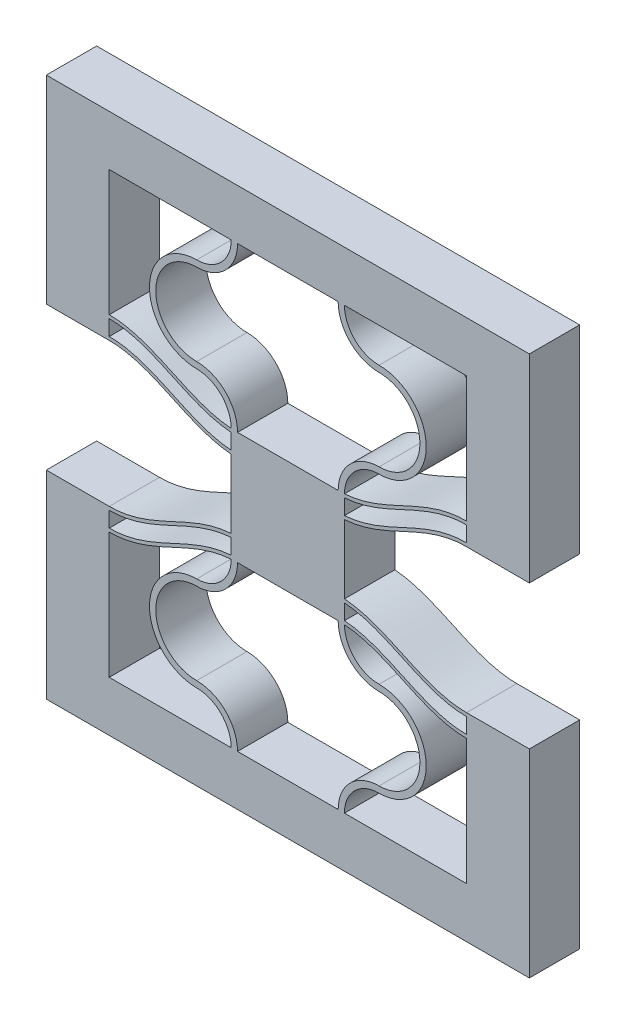
SolidWorks part; units mm, degrees
ref_plane "Front Plane" through (0, 0, 0) normal (0, 0, 1) x (1, 0, 0)
ref_plane "Top Plane" through (0, 0, 0) normal (0, 1, 0) x (1, 0, 0)
ref_plane "Right Plane" through (0, 0, 0) normal (1, 0, 0) x (0, 0, -1)
sketch "Sketch1" plane through (0, 0, 0) normal (0, 0, 1) x (1, 0, 0)
  line L4 (0, 10) -> (0, 0)
  line L5 (10.2, 0) -> (10.2, 13) construction
  line L6 (10.2, 13) -> (10.2, 15.9822) construction
  line L17 (9.7, 0) -> (0, 0)
  line L18 (10.7, 0) -> (20.4, 0)
  line L19 (20.4, 0) -> (20.4, 10)
  line L20 (10.7001, 13.2522) -> (10.7001, 14.4822)
  line L21 (9.6999, 13.2522) -> (9.6999, 14.4822)
  line L22 (10.7001, 14.7522) -> (10.7001, 15.9822)
  line L23 (10.7001, 15.9822) -> (9.6999, 15.9822)
  line L24 (9.6999, 15.9822) -> (9.6999, 14.7522)
  line L31 (-5, 11.77) -> (-5, -4)
  line L32 (-5, -4) -> (25.4, -4)
  line L33 (25.4, -4) -> (25.4, 11.77)
  line L34 (0, 10.27) -> (0, 11.5)
  line L36 (-5, 11.77) -> (0, 11.77)
  line L37 (25.4, 11.77) -> (20.4, 11.77)
  line L38 (20.4, 10.27) -> (20.4, 11.5)
  arc A0 (10.2, 13) -> (6.95, 9.75) centre (6.95, 13) cw
  arc A1 (6.95, 9.75) -> (6.95, 3.25) centre (6.95, 6.5) ccw
  arc A2 (6.95, 3.25) -> (10.2, 0) centre (6.95, 0) cw
  arc A3 (9.6999, 12.9822) -> (6.95, 10.25) centre (6.95, 13) cw
  arc A4 (6.95, 10.25) -> (6.95, 2.75) centre (6.95, 6.5) ccw
  arc A5 (6.95, 2.75) -> (9.7, 0) centre (6.95, 0) cw
  arc A6 (9.7, 13) -> (6.95, 10.25) centre (6.95, 13) cw construction
  arc A7 (13.45, 3.25) -> (10.2, 0) centre (13.45, 0) ccw
  arc A8 (13.45, 2.75) -> (10.7, 0) centre (13.45, 0) ccw
  arc A9 (13.45, 9.75) -> (13.45, 3.25) centre (13.45, 6.5) cw
  arc A10 (13.45, 10.25) -> (13.45, 2.75) centre (13.45, 6.5) cw
  arc A11 (10.7001, 12.9822) -> (13.45, 10.25) centre (13.45, 13) ccw
  arc A12 (10.2, 13) -> (13.45, 9.75) centre (13.45, 13) ccw
  spline S0 degree 4 poles (-2.0403, 10.5565) (-1.977, 10.5394) (-1.8508, 10.5065) (-1.6651, 10.4606) (-1.4028, 10.4071) (-1.1002, 10.3505) (-0.7494, 10.3082) (-0.4826, 10.2809) (-0.0963, 10.2698) (0.0504, 10.2691) (0.3002, 10.2751) (0.4954, 10.2862) (0.6898, 10.3027) (0.8874, 10.3246) (1.1319, 10.3584) (1.4241, 10.409) (1.7623, 10.4818) (2.2204, 10.602) (2.7465, 10.7686) (3.2637, 10.961) (3.7735, 11.1717) (4.2072, 11.3616) (4.5674, 11.5244) (4.9265, 11.6897) (5.2852, 11.8557) (5.734, 12.0622) (6.4147, 12.3676) (7.1961, 12.6896) (8.0933, 12.9875) (9.0168, 13.1885) (9.8039, 13.2774) (10.5961, 13.2774) (11.3832, 13.1885) (12.3067, 12.9875) (13.2039, 12.6896) (13.9853, 12.3676) (14.666, 12.0622) (15.1148, 11.8557) (15.4735, 11.6897) (15.8327, 11.5244) (16.1927, 11.3616) (16.6268, 11.1717) (17.1359, 10.961) (17.7469, 10.7341) (18.3679, 10.5443) (18.928, 10.4147) (19.4122, 10.3342) (19.7634, 10.2959) (20.0425, 10.2765) (20.3499, 10.2691) (20.4953, 10.2698) (20.8095, 10.2786) (21.0299, 10.2972) (21.302, 10.325) (21.5503, 10.3617) (21.8089, 10.4071) (22.0615, 10.4606) (22.2517, 10.5065) (22.3773, 10.5394) (22.4399, 10.5565) knots 0 0 0 0 0 0.010159 0.020319 0.030478 0.040638 0.060704 0.070737 0.080771 0.088497 0.096222 0.103948 0.111674 0.1194 0.127126 0.142578 0.15803 0.173482 0.201155 0.228828 0.24428 0.259732 0.275184 0.290636 0.306088 0.32154 0.352443 0.407289 0.438193 0.469096 0.5 0.530904 0.561807 0.592711 0.647557 0.67846 0.693912 0.709364 0.724816 0.740268 0.75572 0.771172 0.798845 0.826518 0.857422 0.872874 0.888326 0.903778 0.911503 0.919229 0.929263 0.939296 0.949329 0.959362 0.969522 0.979681 0.989841 1 1 1 1 1 construction
  spline S1 degree 4 poles (0, 10.27) (0.0414, 10.27) (0.1259, 10.2709) (0.3002, 10.2751) (0.4954, 10.2862) (0.6898, 10.3027) (0.8874, 10.3246) (1.1319, 10.3584) (1.4241, 10.409) (1.7623, 10.4818) (2.2204, 10.602) (2.7465, 10.7686) (3.2637, 10.961) (3.7735, 11.1717) (4.2072, 11.3616) (4.5674, 11.5244) (4.9265, 11.6897) (5.2852, 11.8557) (5.734, 12.0622) (6.4147, 12.3676) (7.1961, 12.6896) (8.0933, 12.9875) (9.0168, 13.1885) (9.8039, 13.2774) (10.5961, 13.2774) (11.3832, 13.1885) (12.3067, 12.9875) (13.2039, 12.6896) (13.9853, 12.3676) (14.666, 12.0622) (15.1148, 11.8557) (15.4735, 11.6897) (15.8327, 11.5244) (16.1927, 11.3616) (16.6268, 11.1717) (17.1359, 10.961) (17.7469, 10.7341) (18.3679, 10.5443) (18.928, 10.4147) (19.4122, 10.3342) (19.7634, 10.2959) (20.0425, 10.2765) (20.2746, 10.2709) (20.3586, 10.27) (20.4, 10.27) knots 0.080771 0.080771 0.080771 0.080771 0.080771 0.088497 0.096222 0.103948 0.111674 0.1194 0.127126 0.142578 0.15803 0.173482 0.201155 0.228828 0.24428 0.259732 0.275184 0.290636 0.306088 0.32154 0.352443 0.407289 0.438193 0.469096 0.5 0.530904 0.561807 0.592711 0.647557 0.67846 0.693912 0.709364 0.724816 0.740268 0.75572 0.771172 0.798845 0.826518 0.857422 0.872874 0.888326 0.903778 0.911503 0.919229 0.919229 0.919229 0.919229 0.919229
  spline S2 degree 4 poles (-2.0403, 11.7865) (-1.977, 11.7694) (-1.8508, 11.7365) (-1.6651, 11.6906) (-1.4028, 11.6371) (-1.1002, 11.5805) (-0.7494, 11.5382) (-0.4826, 11.5109) (-0.0963, 11.4998) (0.0504, 11.4991) (0.3002, 11.5051) (0.4954, 11.5162) (0.6898, 11.5327) (0.8874, 11.5546) (1.1319, 11.5884) (1.4241, 11.639) (1.7623, 11.7118) (2.2204, 11.832) (2.7465, 11.9986) (3.2637, 12.191) (3.7735, 12.4017) (4.2072, 12.5916) (4.5674, 12.7544) (4.9265, 12.9197) (5.2852, 13.0857) (5.734, 13.2922) (6.4147, 13.5976) (7.1961, 13.9196) (8.0933, 14.2175) (9.0168, 14.4185) (9.8039, 14.5074) (10.5961, 14.5074) (11.3832, 14.4185) (12.3067, 14.2175) (13.2039, 13.9196) (13.9853, 13.5976) (14.666, 13.2922) (15.1148, 13.0857) (15.4735, 12.9197) (15.8327, 12.7544) (16.1927, 12.5916) (16.6268, 12.4017) (17.1359, 12.191) (17.7469, 11.9641) (18.3679, 11.7743) (18.928, 11.6447) (19.4122, 11.5642) (19.7634, 11.5259) (20.0425, 11.5065) (20.3499, 11.4991) (20.4953, 11.4998) (20.8095, 11.5086) (21.0299, 11.5272) (21.302, 11.555) (21.5503, 11.5917) (21.8089, 11.6371) (22.0615, 11.6906) (22.2517, 11.7365) (22.3773, 11.7694) (22.4399, 11.7865) knots 0 0 0 0 0 0.010159 0.020319 0.030478 0.040638 0.060704 0.070737 0.080771 0.088497 0.096222 0.103948 0.111674 0.1194 0.127126 0.142578 0.15803 0.173482 0.201155 0.228828 0.24428 0.259732 0.275184 0.290636 0.306088 0.32154 0.352443 0.407289 0.438193 0.469096 0.5 0.530904 0.561807 0.592711 0.647557 0.67846 0.693912 0.709364 0.724816 0.740268 0.75572 0.771172 0.798845 0.826518 0.857422 0.872874 0.888326 0.903778 0.911503 0.919229 0.929263 0.939296 0.949329 0.959362 0.969522 0.979681 0.989841 1 1 1 1 1 construction
  spline S3 degree 4 poles (0, 11.5) (0.0414, 11.5) (0.1259, 11.5009) (0.3002, 11.5051) (0.4954, 11.5162) (0.6898, 11.5327) (0.8874, 11.5546) (1.1319, 11.5884) (1.4241, 11.639) (1.7623, 11.7118) (2.2204, 11.832) (2.7465, 11.9986) (3.2637, 12.191) (3.7735, 12.4017) (4.2072, 12.5916) (4.5674, 12.7544) (4.9265, 12.9197) (5.2852, 13.0857) (5.734, 13.2922) (6.4147, 13.5976) (7.1961, 13.9196) (8.0933, 14.2175) (9.0168, 14.4185) (9.8039, 14.5074) (10.5961, 14.5074) (11.3832, 14.4185) (12.3067, 14.2175) (13.2039, 13.9196) (13.9853, 13.5976) (14.666, 13.2922) (15.1148, 13.0857) (15.4735, 12.9197) (15.8327, 12.7544) (16.1927, 12.5916) (16.6268, 12.4017) (17.1359, 12.191) (17.7469, 11.9641) (18.3679, 11.7743) (18.928, 11.6447) (19.4122, 11.5642) (19.7634, 11.5259) (20.0425, 11.5065) (20.2746, 11.5009) (20.3586, 11.5) (20.4, 11.5) knots 0.080771 0.080771 0.080771 0.080771 0.080771 0.088497 0.096222 0.103948 0.111674 0.1194 0.127126 0.142578 0.15803 0.173482 0.201155 0.228828 0.24428 0.259732 0.275184 0.290636 0.306088 0.32154 0.352443 0.407289 0.438193 0.469096 0.5 0.530904 0.561807 0.592711 0.647557 0.67846 0.693912 0.709364 0.724816 0.740268 0.75572 0.771172 0.798845 0.826518 0.857422 0.872874 0.888326 0.903778 0.911503 0.919229 0.919229 0.919229 0.919229 0.919229
  spline S4 degree 4 poles (-2.0403, 12.0565) (-1.977, 12.0394) (-1.8508, 12.0065) (-1.6651, 11.9606) (-1.4028, 11.9071) (-1.1002, 11.8505) (-0.7494, 11.8082) (-0.4826, 11.7809) (-0.0963, 11.7698) (0.0504, 11.7691) (0.3002, 11.7751) (0.4954, 11.7862) (0.6898, 11.8027) (0.8874, 11.8246) (1.1319, 11.8584) (1.4241, 11.909) (1.7623, 11.9818) (2.2204, 12.102) (2.7465, 12.2686) (3.2637, 12.461) (3.7735, 12.6717) (4.2072, 12.8616) (4.5674, 13.0244) (4.9265, 13.1897) (5.2852, 13.3557) (5.734, 13.5622) (6.4147, 13.8676) (7.1961, 14.1896) (8.0933, 14.4875) (9.0168, 14.6885) (9.8039, 14.7774) (10.5961, 14.7774) (11.3832, 14.6885) (12.3067, 14.4875) (13.2039, 14.1896) (13.9853, 13.8676) (14.666, 13.5622) (15.1148, 13.3557) (15.4735, 13.1897) (15.8327, 13.0244) (16.1927, 12.8616) (16.6268, 12.6717) (17.1359, 12.461) (17.7469, 12.2341) (18.3679, 12.0443) (18.928, 11.9147) (19.4122, 11.8342) (19.7634, 11.7959) (20.0425, 11.7765) (20.3499, 11.7691) (20.4953, 11.7698) (20.8095, 11.7786) (21.0299, 11.7972) (21.302, 11.825) (21.5503, 11.8617) (21.8089, 11.9071) (22.0615, 11.9606) (22.2517, 12.0065) (22.3773, 12.0394) (22.4399, 12.0565) knots 0 0 0 0 0 0.010159 0.020319 0.030478 0.040638 0.060704 0.070737 0.080771 0.088497 0.096222 0.103948 0.111674 0.1194 0.127126 0.142578 0.15803 0.173482 0.201155 0.228828 0.24428 0.259732 0.275184 0.290636 0.306088 0.32154 0.352443 0.407289 0.438193 0.469096 0.5 0.530904 0.561807 0.592711 0.647557 0.67846 0.693912 0.709364 0.724816 0.740268 0.75572 0.771172 0.798845 0.826518 0.857422 0.872874 0.888326 0.903778 0.911503 0.919229 0.929263 0.939296 0.949329 0.959362 0.969522 0.979681 0.989841 1 1 1 1 1 construction
  spline S5 degree 4 poles (0, 11.77) (0.0414, 11.77) (0.1259, 11.7709) (0.3002, 11.7751) (0.4954, 11.7862) (0.6898, 11.8027) (0.8874, 11.8246) (1.1319, 11.8584) (1.4241, 11.909) (1.7623, 11.9818) (2.2204, 12.102) (2.7465, 12.2686) (3.2637, 12.461) (3.7735, 12.6717) (4.2072, 12.8616) (4.5674, 13.0244) (4.9265, 13.1897) (5.2852, 13.3557) (5.734, 13.5622) (6.4147, 13.8676) (7.1961, 14.1896) (8.0933, 14.4875) (9.0168, 14.6885) (9.8039, 14.7774) (10.5961, 14.7774) (11.3832, 14.6885) (12.3067, 14.4875) (13.2039, 14.1896) (13.9853, 13.8676) (14.666, 13.5622) (15.1148, 13.3557) (15.4735, 13.1897) (15.8327, 13.0244) (16.1927, 12.8616) (16.6268, 12.6717) (17.1359, 12.461) (17.7469, 12.2341) (18.3679, 12.0443) (18.928, 11.9147) (19.4122, 11.8342) (19.7634, 11.7959) (20.0425, 11.7765) (20.2746, 11.7709) (20.3586, 11.77) (20.4, 11.77) knots 0.080771 0.080771 0.080771 0.080771 0.080771 0.088497 0.096222 0.103948 0.111674 0.1194 0.127126 0.142578 0.15803 0.173482 0.201155 0.228828 0.24428 0.259732 0.275184 0.290636 0.306088 0.32154 0.352443 0.407289 0.438193 0.469096 0.5 0.530904 0.561807 0.592711 0.647557 0.67846 0.693912 0.709364 0.724816 0.740268 0.75572 0.771172 0.798845 0.826518 0.857422 0.872874 0.888326 0.903778 0.911503 0.919229 0.919229 0.919229 0.919229 0.919229
  spline S8 degree 4 poles (-2.0403, 10.2865) (-1.977, 10.2694) (-1.8508, 10.2365) (-1.6651, 10.1906) (-1.4028, 10.1371) (-1.1002, 10.0805) (-0.7494, 10.0382) (-0.4826, 10.0109) (-0.0963, 9.9998) (0.0504, 9.9991) (0.3002, 10.0051) (0.4954, 10.0162) (0.6898, 10.0327) (0.8874, 10.0546) (1.1319, 10.0884) (1.4241, 10.139) (1.7623, 10.2118) (2.2204, 10.332) (2.7465, 10.4986) (3.2637, 10.691) (3.7735, 10.9017) (4.2072, 11.0916) (4.5674, 11.2544) (4.9265, 11.4197) (5.2852, 11.5857) (5.734, 11.7922) (6.4147, 12.0976) (7.1961, 12.4196) (8.0933, 12.7175) (9.0168, 12.9185) (9.8039, 13.0074) (10.5961, 13.0074) (11.3832, 12.9185) (12.3067, 12.7175) (13.2039, 12.4196) (13.9853, 12.0976) (14.666, 11.7922) (15.1148, 11.5857) (15.4735, 11.4197) (15.8327, 11.2544) (16.1927, 11.0916) (16.6268, 10.9017) (17.1359, 10.691) (17.7469, 10.4641) (18.3679, 10.2743) (18.928, 10.1447) (19.4122, 10.0642) (19.7634, 10.0259) (20.0425, 10.0065) (20.3499, 9.9991) (20.4953, 9.9998) (20.8095, 10.0086) (21.0299, 10.0272) (21.302, 10.055) (21.5503, 10.0917) (21.8089, 10.1371) (22.0615, 10.1906) (22.2517, 10.2365) (22.3773, 10.2694) (22.4399, 10.2865) knots 0 0 0 0 0 0.010159 0.020319 0.030478 0.040638 0.060704 0.070737 0.080771 0.088497 0.096222 0.103948 0.111674 0.1194 0.127126 0.142578 0.15803 0.173482 0.201155 0.228828 0.24428 0.259732 0.275184 0.290636 0.306088 0.32154 0.352443 0.407289 0.438193 0.469096 0.5 0.530904 0.561807 0.592711 0.647557 0.67846 0.693912 0.709364 0.724816 0.740268 0.75572 0.771172 0.798845 0.826518 0.857422 0.872874 0.888326 0.903778 0.911503 0.919229 0.929263 0.939296 0.949329 0.959362 0.969522 0.979681 0.989841 1 1 1 1 1 construction
  spline S9 degree 4 poles (0, 10) (0.0414, 10) (0.1259, 10.0009) (0.3002, 10.0051) (0.4954, 10.0162) (0.6898, 10.0327) (0.8874, 10.0546) (1.1319, 10.0884) (1.4241, 10.139) (1.7623, 10.2118) (2.2204, 10.332) (2.7465, 10.4986) (3.2637, 10.691) (3.7735, 10.9017) (4.2072, 11.0916) (4.5674, 11.2544) (4.9265, 11.4197) (5.2852, 11.5857) (5.734, 11.7922) (6.4147, 12.0976) (7.1961, 12.4196) (8.0933, 12.7175) (9.0168, 12.9185) (9.8039, 13.0074) (10.5961, 13.0074) (11.3832, 12.9185) (12.3067, 12.7175) (13.2039, 12.4196) (13.9853, 12.0976) (14.666, 11.7922) (15.1148, 11.5857) (15.4735, 11.4197) (15.8327, 11.2544) (16.1927, 11.0916) (16.6268, 10.9017) (17.1359, 10.691) (17.7469, 10.4641) (18.3679, 10.2743) (18.928, 10.1447) (19.4122, 10.0642) (19.7634, 10.0259) (20.0425, 10.0065) (20.2746, 10.0009) (20.3586, 10) (20.4, 10) knots 0.080771 0.080771 0.080771 0.080771 0.080771 0.088497 0.096222 0.103948 0.111674 0.1194 0.127126 0.142578 0.15803 0.173482 0.201155 0.228828 0.24428 0.259732 0.275184 0.290636 0.306088 0.32154 0.352443 0.407289 0.438193 0.469096 0.5 0.530904 0.561807 0.592711 0.647557 0.67846 0.693912 0.709364 0.724816 0.740268 0.75572 0.771172 0.798845 0.826518 0.857422 0.872874 0.888326 0.903778 0.911503 0.919229 0.919229 0.919229 0.919229 0.919229
  dimension "D4" = 0.27
  dimension "D6" = 4
  dimension "D1" = 13
  dimension "D2" = 0.5
  dimension "D3" = 0.27
  dimension "D7" = 5
  dimension "D5" = 1.5
extrude "Boss-Extrude1" add sketch "Sketch1" along normal blind 4
sketch "Sketch4" plane through (0, 15.9822, 0) normal (0, 1, 0) x (1, 0, 0)
  line L24 (10.7001, 0) -> (9.6999, 0)
  line L25 (9.6999, 0) -> (9.6999, -4)
  line L26 (10.7001, 0) -> (9.6999, 0)
  line L27 (10.7001, -4) -> (10.7001, 0)
  line L29 (9.6999, 0) -> (9.6999, -4)
  line L31 (10.7001, -4) -> (10.7001, 0)
  line L32 (9.6999, -4) -> (10.7001, -4)
  line L33 (9.6999, -4) -> (10.7001, -4)
  dimension "D1" = 0
extrude "Boss-Extrude2" add sketch "Sketch4" along normal blind 1.5
mirror "Mirror3" about plane through (0, 17.4822, 0) normal (0, 1, 0) of bodies 179
ref_plane "Plane1" through (10.2, 0, 0) normal (-1, 0, 0) x (0, 0, 1)
split "Split2" trim tools "Plane1" bodies to split 247 102 resulting bodies 225
sketch "Sketch7" plane through (10.2, 0, 0) normal (-1, 0, 0) x (0, 0, 1)
  line L4 (4, 34.9645) -> (4, 38.9645)
  line L12 (0, 13) -> (4, 13)
  line L13 (0, 13) -> (4, 13)
  line L14 (4, 13) -> (4, 21.9645)
  line L15 (4, 13) -> (4, 21.9645)
  line L20 (4, 0) -> (0, 0)
  line L22 (4, 0) -> (0, 0)
  line L23 (0, -4) -> (4, -4)
  line L27 (0, -4) -> (4, -4)
  line L31 (4, 21.9645) -> (0, 21.9645)
  line L32 (4, 21.9645) -> (0, 21.9645)
  line L33 (0, 21.9645) -> (0, 13)
  line L34 (0, 21.9645) -> (0, 13)
  line L36 (4, -4) -> (4, 0)
  line L38 (4, 34.9645) -> (4, 38.9645)
  line L39 (4, 34.9645) -> (4, 38.9645)
  line L40 (4, 38.9645) -> (0, 38.9645)
  line L41 (4, 38.9645) -> (0, 38.9645)
  line L46 (4, 34.9645) -> (4, 38.9645)
  line L51 (0, 38.9645) -> (0, 34.9645)
  line L52 (0, 38.9645) -> (0, 34.9645)
  line L53 (0, 34.9645) -> (4, 34.9645)
  line L54 (0, 34.9645) -> (4, 34.9645)
  line L55 (4, 38.9645) -> (0, 38.9645)
  line L57 (4, 38.9645) -> (0, 38.9645)
  line L59 (4, -4) -> (4, 0)
  line L60 (0, 0) -> (0, -4)
  line L61 (0, 0) -> (0, -4)
  line L62 (0, 38.9645) -> (0, 34.9645)
  line L63 (0, 38.9645) -> (0, 34.9645)
  line L64 (0, 34.9645) -> (4, 34.9645)
  line L65 (0, 34.9645) -> (4, 34.9645)
  dimension "D1" = 0
  dimension "D2" = 0
  dimension "D3" = 0
  dimension "D4" = 0
extrude "Boss-Extrude3" add sketch "Sketch7" along normal blind 4
mirror "Mirror2" about plane through (6.2, 0, 0) normal (-1, 0, 0) of bodies 226
